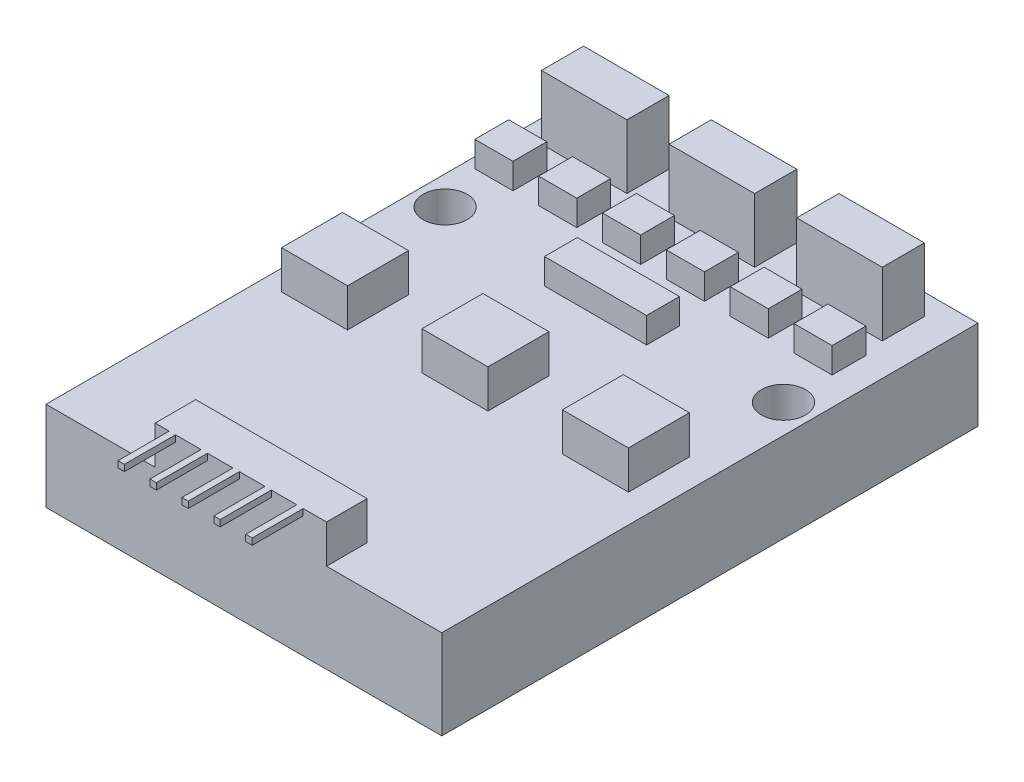
SolidWorks part; units mm, degrees
ref_plane "前基準面" through (0, 0, 0) normal (0, 0, 1) x (1, 0, 0)
ref_plane "上基準面" through (0, 0, 0) normal (0, 1, 0) x (1, 0, 0)
ref_plane "右基準面" through (0, 0, 0) normal (1, 0, 0) x (0, 0, -1)
sketch "草圖1" plane through (0, 0, 0) normal (0, 1, 0) x (1, 0, 0)
  line L1 (0, 0) -> (31, 0)
  line L2 (0, 0) -> (0, 42)
  line L3 (0, 42) -> (31, 42)
  line L4 (31, 0) -> (31, 42)
  dimension "D1" = 42
  dimension "D2" = 31
extrude "填料-伸長1" add sketch "草圖1" along normal blind 7
sketch "草圖3" plane through (0, 7, 0) normal (0, 1, 0) x (1, 0, 0)
  line L0 (11.7588, 40.3463) -> (11.7588, 37.0436)
  line L1 (1.7588, 40.3463) -> (8.4586, 40.3463)
  line L2 (1.7588, 40.3463) -> (1.7588, 37.0436)
  line L3 (1.7588, 37.0436) -> (8.4586, 37.0436)
  line L4 (8.4586, 40.3463) -> (8.4586, 37.0436)
  line L5 (11.7588, 40.3463) -> (18.4586, 40.3463)
  line L6 (18.4586, 40.3463) -> (18.4586, 37.0436)
  line L7 (11.7588, 37.0436) -> (18.4586, 37.0436)
  line L8 (21.7588, 40.3463) -> (21.7588, 37.0436)
  line L9 (21.7588, 40.3463) -> (28.4586, 40.3463)
  line L10 (28.4586, 40.3463) -> (28.4586, 37.0436)
  line L11 (21.7588, 37.0436) -> (28.4586, 37.0436)
  dimension "D1" = 3
extrude "填料-伸長2" add sketch "草圖3" along normal blind 5
sketch "草圖4" plane through (0, 7, 0) normal (0, 1, 0) x (1, 0, 0)
  line L0 (5.8228, 35.4181) -> (5.8228, 32.7652)
  line L1 (0.8228, 35.4181) -> (3.8073, 35.4181)
  line L2 (0.8228, 35.4181) -> (0.8228, 32.7652)
  line L3 (0.8228, 32.7652) -> (3.8073, 32.7652)
  line L4 (3.8073, 35.4181) -> (3.8073, 32.7652)
  line L5 (5.8228, 35.4181) -> (8.8073, 35.4181)
  line L6 (8.8073, 35.4181) -> (8.8073, 32.7652)
  line L7 (5.8228, 32.7652) -> (8.8073, 32.7652)
  line L8 (10.8228, 35.4181) -> (10.8228, 32.7652)
  line L9 (10.8228, 35.4181) -> (13.8073, 35.4181)
  line L10 (13.8073, 35.4181) -> (13.8073, 32.7652)
  line L11 (10.8228, 32.7652) -> (13.8073, 32.7652)
  line L12 (15.8228, 35.4181) -> (15.8228, 32.7652)
  line L13 (15.8228, 35.4181) -> (18.8073, 35.4181)
  line L14 (18.8073, 35.4181) -> (18.8073, 32.7652)
  line L15 (15.8228, 32.7652) -> (18.8073, 32.7652)
  line L16 (20.8228, 35.4181) -> (20.8228, 32.7652)
  line L17 (20.8228, 35.4181) -> (23.8073, 35.4181)
  line L18 (23.8073, 35.4181) -> (23.8073, 32.7652)
  line L19 (20.8228, 32.7652) -> (23.8073, 32.7652)
  line L20 (25.8228, 35.4181) -> (25.8228, 32.7652)
  line L21 (25.8228, 35.4181) -> (28.8073, 35.4181)
  line L22 (28.8073, 35.4181) -> (28.8073, 32.7652)
  line L23 (25.8228, 32.7652) -> (28.8073, 32.7652)
  dimension "D1" = 6
extrude "填料-伸長3" add sketch "草圖4" along normal blind 2
sketch "草圖5" plane through (0, 7, 0) normal (0, 1, 0) x (1, 0, 0)
  line L0 (15.5, 42) -> (15.5, 14.9894) construction
  line L1 (31, 42) -> (0, 42) construction
  line L3 (11.5, 30.1165) -> (19.5, 30.1165)
  line L4 (11.5, 30.1165) -> (11.5, 27.5403)
  line L5 (11.5, 27.5403) -> (19.5, 27.5403)
  line L6 (19.5, 30.1165) -> (19.5, 27.5403)
  point P8 (11.5, 28.8284)
  dimension "D1" = 4
  dimension "D2" = 8
extrude "填料-伸長4" add sketch "草圖5" along normal blind 2
sketch "草圖6" plane through (0, 7, 0) normal (0, 1, 0) x (1, 0, 0)
  line L0 (15.5, 42) -> (15.5, 21.6423) construction
  line L1 (31, 42) -> (0, 42) construction
  circle A0 centre (2.25, 29.0111) radius 1.727
  circle A1 centre (28.75, 29.0111) radius 1.727
  dimension "D1" = 26.5
extrude "除料-伸長1" cut sketch "草圖6" against normal through all
sketch "草圖7" plane through (0, 7, 0) normal (0, 1, 0) x (1, 0, 0)
  line L0 (12.6007, 21.6202) -> (12.6007, 16.845)
  line L1 (1.6007, 21.6202) -> (6.7738, 21.6202)
  line L2 (1.6007, 21.6202) -> (1.6007, 16.845)
  line L3 (1.6007, 16.845) -> (6.7738, 16.845)
  line L4 (6.7738, 21.6202) -> (6.7738, 16.845)
  line L5 (12.6007, 21.6202) -> (17.7738, 21.6202)
  line L6 (17.7738, 21.6202) -> (17.7738, 16.845)
  line L7 (12.6007, 16.845) -> (17.7738, 16.845)
  line L8 (23.6007, 21.6202) -> (23.6007, 16.845)
  line L9 (23.6007, 21.6202) -> (28.7738, 21.6202)
  line L10 (28.7738, 21.6202) -> (28.7738, 16.845)
  line L11 (23.6007, 16.845) -> (28.7738, 16.845)
  line L12 (0, 0) -> (31, 0) construction
  line L13 (8.5527, 0) -> (21.9744, 0)
  line L14 (8.5527, 0) -> (8.5527, 3.1753)
  line L15 (8.5527, 3.1753) -> (21.9744, 3.1753)
  line L16 (21.9744, 0) -> (21.9744, 3.1753)
  dimension "D1" = 3
extrude "填料-伸長5" add sketch "草圖7" along normal blind 3
sketch "草圖8" plane through (0, 0, 0) normal (0, 0, 1) x (1, 0, 0)
  line L0 (8.5527, 10) -> (21.9744, 10) construction
  line L1 (9.6456, 10) -> (10.1456, 10)
  line L2 (9.6456, 10) -> (9.6456, 9.5)
  line L3 (9.6456, 9.5) -> (10.1456, 9.5)
  line L4 (10.1456, 10) -> (10.1456, 9.5)
  line L5 (12.1456, 9.5) -> (12.6456, 9.5)
  line L6 (12.1456, 10) -> (12.1456, 9.5)
  line L7 (12.1456, 10) -> (12.6456, 10)
  line L8 (12.6456, 10) -> (12.6456, 9.5)
  line L9 (14.6456, 9.5) -> (15.1456, 9.5)
  line L10 (14.6456, 10) -> (14.6456, 9.5)
  line L11 (14.6456, 10) -> (15.1456, 10)
  line L12 (15.1456, 10) -> (15.1456, 9.5)
  line L13 (17.1456, 9.5) -> (17.6456, 9.5)
  line L14 (17.1456, 10) -> (17.1456, 9.5)
  line L15 (17.1456, 10) -> (17.6456, 10)
  line L16 (17.6456, 10) -> (17.6456, 9.5)
  line L17 (19.6456, 9.5) -> (20.1456, 9.5)
  line L18 (19.6456, 10) -> (19.6456, 9.5)
  line L19 (19.6456, 10) -> (20.1456, 10)
  line L20 (20.1456, 10) -> (20.1456, 9.5)
  dimension "D2" = 0.5
  dimension "D3" = 0.5
  dimension "D1" = 5
extrude "填料-伸長6" add sketch "草圖8" along normal blind 4
